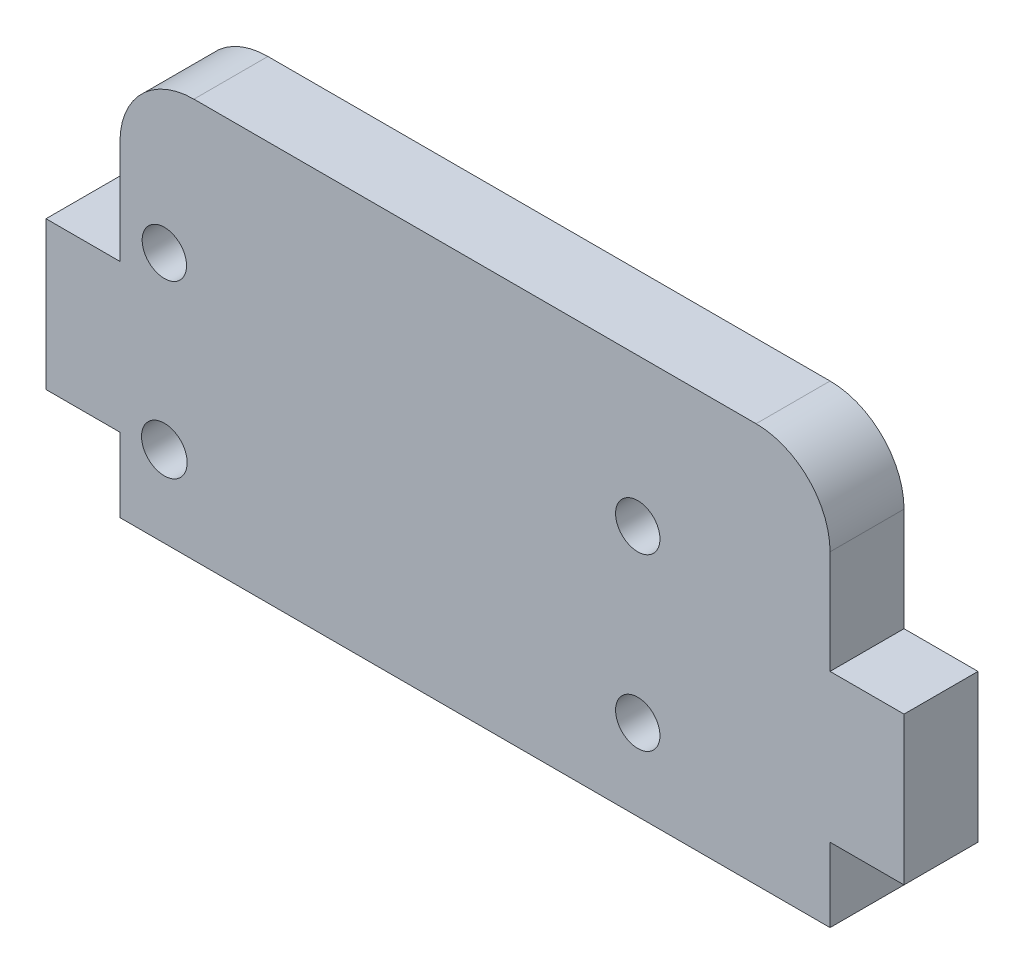
SolidWorks part; units mm, degrees
material "Acrylic (Medium-high impact)"
ref_plane "Front Plane" through (0, 0, 0) normal (0, 0, 1) x (1, 0, 0)
ref_plane "Top Plane" through (0, 0, 0) normal (0, 1, 0) x (1, 0, 0)
ref_plane "Right Plane" through (0, 0, 0) normal (1, 0, 0) x (0, 0, -1)
sketch "Sketch1" plane through (0, 0, 0) normal (0, 0, 1) x (1, 0, 0)
  line L0 (-19.7335, 0) -> (28.2665, 0)
  line L1 (28.2665, 0) -> (28.2665, 5)
  line L2 (-19.7335, 0) -> (-19.7335, 5)
  line L3 (-19.7335, 27) -> (28.2665, 27)
  line L4 (28.2665, 5) -> (33.2665, 5)
  line L5 (33.2665, 5) -> (33.2665, 15)
  line L6 (33.2665, 15) -> (28.2665, 15)
  line L7 (4.2665, 0) -> (4.2665, 27) construction
  line L8 (-19.7335, 5) -> (-24.7335, 5)
  line L9 (-24.7335, 5) -> (-24.7335, 15)
  line L10 (-24.7335, 15) -> (-19.7335, 15)
  line L11 (-19.7335, 15) -> (-19.7335, 27)
  line L12 (28.2665, 15) -> (28.2665, 27)
  line L13 (13.2665, 27) -> (13.2665, 0) construction
  line L14 (28.2665, 17) -> (-19.7335, 17) construction
  line L15 (33.2665, 7) -> (-24.7335, 7) construction
  line L16 (-16.7335, 27) -> (-16.7335, 0) construction
  circle A2 centre (-16.7335, 17) radius 1.5
  circle A4 centre (-16.7335, 5.4886) radius 1.5429
  circle A5 centre (15.2665, 17) radius 1.5
  circle A6 centre (15.2665, 5.4886) radius 1.5
  dimension "D12" = 3
  dimension "D1" = 27
  dimension "D2" = 48
  dimension "D3" = 5
  dimension "D4" = 10
  dimension "D5" = 5
  dimension "D6" = 15
  dimension "D7" = 10
  dimension "D8" = 10
  dimension "D11" = 30
extrude "Boss-Extrude1" add sketch "Sketch1" along normal blind 5
fillet "Fillet1" radius 5 1 edges at (-19.7335, 27, 2.5)
fillet "Fillet2" radius 5 1 edges at (28.2665, 27, 2.5)
